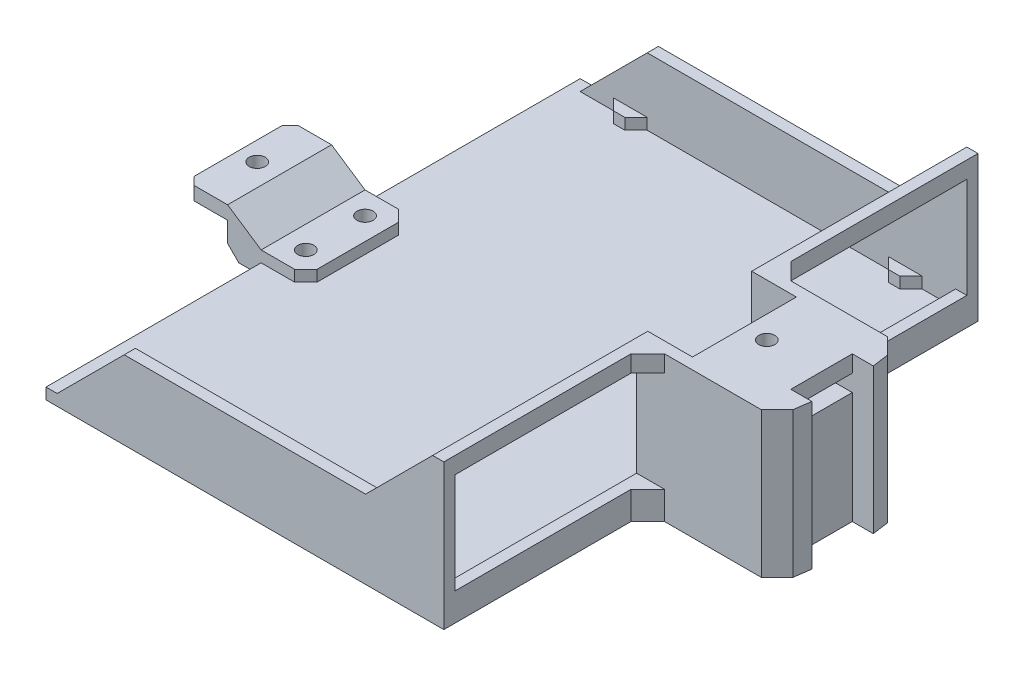
SolidWorks part; units mm, degrees
ref_plane "Front Plane" through (0, 0, 0) normal (0, 0, 1) x (1, 0, 0)
ref_plane "Top Plane" through (0, 0, 0) normal (0, 1, 0) x (1, 0, 0)
ref_plane "Right Plane" through (0, 0, 0) normal (1, 0, 0) x (0, 0, -1)
sketch "Sketch1" plane through (0, 0, 0) normal (0, 1, 0) x (1, 0, 0)
  line L0 (-1000, 0) -> (49000, 0) construction
  line L1 (6.985, -70.358) -> (-6.985, -70.358)
  line L6 (70.358, 6.985) -> (75.1332, 6.985)
  line L7 (70.358, 6.985) -> (70.358, -6.985)
  line L8 (70.358, -6.985) -> (75.1332, -6.985)
  line L9 (75.1332, 6.985) -> (75.1332, -6.985)
  line L10 (6.985, -70.358) -> (6.985, -75.1332)
  line L11 (6.985, -75.1332) -> (-6.985, -75.1332)
  line L12 (-6.985, -70.358) -> (-6.985, -75.1332)
  line L13 (-70.358, -6.985) -> (-70.358, 6.985)
  line L14 (-70.358, -6.985) -> (-75.1332, -6.985)
  line L15 (-75.1332, -6.985) -> (-75.1332, 6.985)
  line L16 (-70.358, 6.985) -> (-75.1332, 6.985)
  line L17 (-6.985, 70.358) -> (6.985, 70.358)
  line L18 (-6.985, 70.358) -> (-6.985, 75.1332)
  line L19 (-6.985, 75.1332) -> (6.985, 75.1332)
  line L20 (6.985, 70.358) -> (6.985, 75.1332)
  circle A0 centre (0, 0) radius 75.692 construction
  circle A1 centre (0, 0) radius 76.2 construction
  point P4 (70.358, 0)
  point P11 (0, 0)
  point P31 (0, 0)
  dimension "D1" = 151.384
  dimension "D2" = 152.4
  dimension "D3" = 13.97
  dimension "D4" = 140.716
  dimension "D6" = 4.7752
  dimension "D7" = 4
sketch "Sketch3" plane through (0, 0, 0) normal (0, 1, 0) x (1, 0, 0)
  line L1 (-45.2113, -60.706) -> (45.2113, -60.706)
  line L2 (-45.2113, -60.706) -> (-45.2113, 60.706)
  line L3 (-45.2113, 60.706) -> (45.2113, 60.706)
  line L4 (45.2113, -60.706) -> (45.2113, 60.706)
  line L5 (-45.2113, -60.706) -> (45.2113, 60.706) construction
  line L6 (-45.2113, 60.706) -> (45.2113, -60.706) construction
  circle A0 centre (0, 0) radius 75.692 construction
  point P0 (0, 0)
  dimension "D1" = 121.412
extrude "Boss-Extrude4" add sketch "Sketch3" along normal blind 2.54
sketch "Sketch6" plane through (0, 2.54, 0) normal (0, 1, 0) x (1, 0, 0)
  line L0 (-1000, 0) -> (49000, 0) construction
  line L1 (45.2113, -60.706) -> (45.2113, 60.706) construction
  line L2 (45.2113, 60.706) -> (-45.2113, 60.706) construction
  line L3 (45.2113, -60.706) -> (45.2113, 60.706)
  line L4 (45.2113, 60.706) -> (-45.2113, 60.706)
  line L5 (-45.2113, 60.706) -> (-45.2113, 58.166)
  line L6 (-45.2113, 60.706) -> (-45.2113, -60.706) construction
  line L7 (-45.2113, 58.166) -> (42.6713, 58.166)
  line L8 (42.6713, 58.166) -> (42.6713, -58.166)
  line L10 (-45.2113, -58.166) -> (42.6713, -58.166)
  line L11 (-45.2113, -60.706) -> (-45.2113, -58.166)
  line L12 (45.2113, -60.706) -> (-45.2113, -60.706)
  dimension "D1" = 2.54
  dimension "D2" = 2.54
extrude "Boss-Extrude5" add sketch "Sketch6" along normal blind 30.48
sketch "Sketch7" plane through (0, 0, 60.706) normal (0, 0, 1) x (1, 0, 0)
  line L0 (42.6713, 2.54) -> (-45.2113, 2.54) construction
  line L1 (42.6713, 33.02) -> (42.6713, 2.54) construction
  line L2 (42.6713, 2.54) -> (-45.2113, 2.54) construction
  line L3 (42.6713, 33.02) -> (42.6713, 2.54) construction
  line L4 (0, -1000) -> (0, 49000) construction
  line L5 (-957.3287, 17.78) -> (49042.6713, 17.78) construction
  line L6 (-42.6713, 33.02) -> (-42.6713, 2.54) construction
  line L7 (-42.6713, 2.54) -> (-27.4313, 17.78)
  line L8 (-27.4313, 17.78) -> (27.4313, 17.78)
  line L9 (27.4313, 17.78) -> (42.6713, 33.02)
  line L10 (42.6713, 33.02) -> (-45.2113, 33.02)
  line L11 (-45.2113, 33.02) -> (-45.2113, 2.54)
  line L12 (-45.2113, 2.54) -> (-42.6713, 2.54)
  point P9 (42.6713, 17.78)
  dimension "D1" = 45
  dimension "D2" = 45
extrude "Cut-Extrude2" cut sketch "Sketch7" against normal through all
sketch "Sketch8" plane through (0, 0, 0) normal (0, 1, 0) x (1, 0, 0)
  line L0 (-1000, 0) -> (49000, 0) construction
  line L1 (45.2113, 14.351) -> (71.0099, 14.351)
  line L2 (45.2113, -60.706) -> (45.2113, 60.706) construction
  line L3 (71.0099, 14.351) -> (74.603, 10.7579)
  line L4 (74.603, 10.7579) -> (75.1332, 6.985)
  line L5 (75.1332, 6.985) -> (70.358, 6.985)
  line L6 (70.358, 6.985) -> (70.358, -6.985)
  line L7 (45.2113, 14.351) -> (45.2113, -14.351)
  line L8 (45.2113, -14.351) -> (71.0099, -14.351)
  line L9 (71.0099, -14.351) -> (74.603, -10.7579)
  line L10 (74.603, -10.7579) -> (75.1332, -6.985)
  line L11 (75.1332, -6.985) -> (70.358, -6.985)
  line L13 (70.358, 6.985) -> (70.358, -6.985) construction
  line L14 (70.358, 6.985) -> (75.1332, 6.985) construction
  point P13 (45.2113, 0)
  point P17 (70.358, 0)
  dimension "D1" = 82
  dimension "D2" = 135
  dimension "D3" = 28.702
  dimension "D4" = 3.81
extrude "Boss-Extrude6" add sketch "Sketch8" along normal up to surface (33.02 mm away) up to face at (43.518, 33.02, 0)
sketch "Sketch9" plane through (0, 33.02, 0) normal (0, 1, 0) x (1, 0, 0)
  line L0 (-1000, 0) -> (49000, 0) construction
  line L1 (52.8313, -11.811) -> (52.8313, 11.811)
  line L2 (52.8313, 11.811) -> (42.6713, 11.811)
  line L3 (42.6713, 58.166) -> (42.6713, -58.166) construction
  line L4 (42.6713, 11.811) -> (42.6713, -11.811)
  line L5 (52.8313, -11.811) -> (42.6713, -11.811)
  line L6 (71.0099, 14.351) -> (45.2113, 14.351) construction
  point P10 (42.6713, 0)
  point P11 (52.8313, 0)
  dimension "D1" = 10.16
  dimension "D2" = 2.54
extrude "Cut-Extrude3" cut sketch "Sketch9" against normal offset from surface (27.94 mm away) 2.54 up to face at (-21.9706, 2.54, 0)
sketch "Sketch11" plane through (0, 2.54, 0) normal (0, 1, 0) x (1, 0, 0)
  line L5 (35.0513, 58.166) -> (27.4313, 58.166)
  line L6 (-42.6713, 58.166) -> (42.6713, 58.166) construction
  line L7 (27.4313, 58.166) -> (29.9713, 55.626)
  line L8 (29.9713, 55.626) -> (32.5113, 55.626)
  line L9 (32.5113, 55.626) -> (35.0513, 58.166)
  line L10 (42.6713, 58.166) -> (42.6713, -58.166) construction
  line L11 (-1000, 0) -> (49000, 0) construction
  line L12 (0, -1000) -> (0, 49000) construction
  line L13 (-29.9713, 55.626) -> (-32.5113, 55.626)
  line L14 (-27.4313, 58.166) -> (-29.9713, 55.626)
  line L15 (-35.0513, 58.166) -> (-27.4313, 58.166)
  line L16 (-32.5113, 55.626) -> (-35.0513, 58.166)
  line L17 (29.9713, -55.626) -> (32.5113, -55.626)
  line L18 (27.4313, -58.166) -> (29.9713, -55.626)
  line L19 (35.0513, -58.166) -> (27.4313, -58.166)
  line L20 (32.5113, -55.626) -> (35.0513, -58.166)
  line L21 (-27.4313, -58.166) -> (-29.9713, -55.626)
  line L22 (-35.0513, -58.166) -> (-27.4313, -58.166)
  line L23 (-32.5113, -55.626) -> (-35.0513, -58.166)
  line L24 (-29.9713, -55.626) -> (-32.5113, -55.626)
  dimension "D1" = 45
  dimension "D2" = 45
  dimension "D3" = 2.54
  dimension "D4" = 2.54
  dimension "D5" = 7.62
extrude "Boss-Extrude7" add sketch "Sketch11" along normal up to surface (2.54 mm away) up to face at (47.7513, 5.08, 0)
sketch "Sketch12" plane through (52.8313, 0, 0) normal (-1, 0, 0) x (0, 0, 1)
  line L0 (11.811, 5.08) -> (11.811, 33.02) construction
  line L1 (11.811, 29.21) -> (-11.811, 29.21)
  line L2 (11.811, 29.21) -> (11.811, 25.4)
  line L3 (11.811, 25.4) -> (-11.811, 25.4)
  line L4 (-11.811, 29.21) -> (-11.811, 25.4)
  line L5 (-11.811, 5.08) -> (-11.811, 33.02) construction
  line L6 (11.811, 33.02) -> (-11.811, 33.02) construction
  dimension "D1" = 3.81
  dimension "D2" = 3.81
extrude "Cut-Extrude4" cut sketch "Sketch12" against normal blind 10.16
sketch "Sketch13" plane through (62.9913, 0, 0) normal (-1, 0, 0) x (0, 0, 1)
  line L0 (11.811, 29.21) -> (-11.811, 29.21) construction
  line L1 (-6.985, 29.21) -> (6.985, 29.21)
  line L2 (-6.985, 29.21) -> (-6.985, 25.4)
  line L3 (-6.985, 25.4) -> (6.985, 25.4)
  line L4 (6.985, 29.21) -> (6.985, 25.4)
  line L5 (-6.985, 33.02) -> (-6.985, 0) construction
  line L6 (-11.811, 25.4) -> (11.811, 25.4) construction
  line L7 (6.985, 33.02) -> (6.985, 0) construction
extrude "Cut-Extrude5" cut sketch "Sketch13" against normal through all
sketch "Sketch15" plane through (0, 0, 0) normal (0, 0, 1) x (1, 0, 0)
  line L0 (0, -1000) -> (0, 49000) construction
  line L2 (62.9913, 29.21) -> (62.9913, 25.4) construction
  line L3 (62.9913, 25.4) -> (52.8313, 25.4) construction
  line L4 (62.9913, 29.21) -> (52.8313, 29.21) construction
  line L5 (62.9913, 25.4) -> (52.8313, 25.4) construction
  line L6 (62.9913, 29.21) -> (62.9913, 25.4) construction
  line L7 (62.9913, 29.21) -> (52.8313, 29.21) construction
  line L8 (-62.9913, 29.21) -> (-52.8313, 29.21) construction
  line L9 (-62.9913, 29.21) -> (-62.9913, 25.4) construction
  line L10 (-62.9913, 25.4) -> (-52.8313, 25.4) construction
  line L11 (-998.1426, 17.78) -> (49001.8574, 17.78) construction
  line L13 (-62.9913, 10.16) -> (-52.8313, 10.16)
  line L14 (-62.9913, 6.35) -> (-62.9913, 10.16)
  line L15 (-62.9913, 6.35) -> (-52.8313, 6.35)
  line L16 (-27.4313, 17.78) -> (27.4313, 17.78) construction
  line L17 (-52.8313, 6.35) -> (-52.8313, 0)
  line L18 (-52.8313, 0) -> (-45.2113, 0)
  line L19 (-45.2113, 0) -> (-45.2113, 2.54)
  line L20 (-45.2113, 2.54) -> (-35.0513, 2.54)
  line L21 (-35.0513, 2.54) -> (-42.6713, 2.54) construction
  line L23 (-35.0513, 2.54) -> (-35.0513, 5.08)
  line L24 (-35.0513, 5.08) -> (-45.2113, 5.08)
  line L25 (-45.2113, 5.08) -> (-52.8313, 10.16)
  line L26 (-27.4313, 5.08) -> (-35.0513, 5.08) construction
  line L27 (52.8313, 5.08) -> (42.6713, 5.08) construction
  line L28 (52.8313, 5.08) -> (42.6713, 5.08) construction
extrude "Boss-Extrude9" add sketch "Sketch15" against normal up to surface and the other way up to surface up to face at (52.8313, 23.1775, -11.811) other way up to face at (52.8313, 23.1775, 11.811)
hole_wizard "CBORE for #6 Pan Head Machine Screw1" positions "Sketch16" profile "Sketch17" counterbore size "#6" standard "ANSI Inch" end condition through all
sketch "Sketch16" plane through (0, 0, 0) normal (0, -1, 0) x (-1, 0, 0)
  line L0 (-47.7513, -988.189) -> (-47.7513, 49011.811) construction
  line L1 (-52.8313, 11.811) -> (-42.6713, 11.811) construction
  line L2 (-1000, 0) -> (49000, 0) construction
  line L3 (40.1313, -988.189) -> (40.1313, 49011.811) construction
  line L4 (45.2113, 11.811) -> (35.0513, 11.811) construction
  line L5 (-1047.7513, 6.731) -> (48952.2487, 6.731) construction
  line L6 (-1047.7513, -6.731) -> (48952.2487, -6.731) construction
  line L7 (-52.8313, 11.811) -> (-42.6713, 1.651) construction
  line L8 (-42.6713, 11.811) -> (-42.6713, -11.811) construction
  point P0 (-47.7513, 6.731)
  point P7 (-47.7513, 11.811)
  point P18 (-47.7513, -6.731)
  point P24 (40.1313, 11.811)
  point P34 (40.1313, 6.731)
  point P36 (40.1313, -6.731)
  dimension "D1" = 45
sketch "Sketch17" plane through (47.7513, 0, -6.731) normal (1, 0, 0) x (0, 0, -1)
  line L0 (0, 0) -> (0, 33.02)
  line L1 (0, 33.02) -> (1.8288, 33.02)
  line L3 (1.8288, 33.02) -> (1.8288, 2.4638)
  line L4 (1.8288, 2.4638) -> (3.7706, 2.4638)
  line L5 (3.7706, 2.4638) -> (3.7706, 0)
  line L7 (3.7706, 0) -> (0, 0)
  line L11 (0, -6.35) -> (0, 107.95) construction
  dimension "Thru Hole Dia." = 3.6576
  dimension "Thru Hole Depth" = 33.02
  dimension "C'Bore Dia." = 7.5413
  dimension "C'Bore Depth" = 2.4638
hole_wizard "#6 Clearance Hole1" positions "Sketch19" profile "Sketch20" hole size "#6" standard "ANSI Inch" end condition through all
sketch "Sketch19" plane through (0, 33.02, 0) normal (0, 1, 0) x (1, 0, 0)
  line L0 (-1000, 0) -> (49000, 0) construction
  line L1 (0, -1000) -> (0, 49000) construction
  line L2 (57.9113, -988.189) -> (57.9113, 49011.811) construction
  line L3 (62.9913, 11.811) -> (52.8313, 11.811) construction
  point P6 (57.9113, 0)
  point P13 (-57.9113, 0)
  point P20 (57.9113, 11.811)
sketch "Sketch20" plane through (-57.9113, 33.02, 0) normal (1, 0, 0) x (0, 0, 1)
  line L0 (0, 0) -> (0, 33.02)
  line L1 (0, 33.02) -> (1.8288, 33.02)
  line L2 (1.8288, 33.02) -> (1.8288, 0)
  line L5 (1.8288, 0) -> (0, 0)
  line L11 (0, -6.35) -> (0, 107.95) construction
  dimension "Thru Hole Dia." = 3.6576
  dimension "Thru Hole Depth" = 33.02
sketch "Sketch21" plane through (42.6713, 0, 0) normal (-1, 0, 0) x (0, 0, 1)
  line L0 (-1058.166, 17.78) -> (48941.834, 17.78) construction
  line L1 (-58.166, 33.02) -> (-58.166, 2.54) construction
  line L2 (0, -1000) -> (0, 49000) construction
  line L3 (-11.811, 0) -> (11.811, 0) construction
  line L9 (-1008.4655, 5.08) -> (48991.5345, 5.08) construction
  line L10 (-58.166, 6.35) -> (-58.166, 29.21)
  line L11 (-11.811, 5.08) -> (11.811, 5.08) construction
  line L14 (-58.166, 29.21) -> (-14.351, 29.21)
  line L15 (-14.351, 29.21) -> (-14.351, 6.35)
  line L18 (-58.166, 6.35) -> (-14.351, 6.35)
  line L20 (58.166, 29.21) -> (14.351, 29.21)
  line L21 (58.166, 6.35) -> (58.166, 29.21)
  line L22 (58.166, 6.35) -> (14.351, 6.35)
  line L23 (14.351, 29.21) -> (14.351, 6.35)
  line L24 (-58.166, 33.02) -> (-58.166, 17.78) construction
  line L25 (-14.351, 33.02) -> (-14.351, 0) construction
  point P5 (-58.166, 17.78)
  point P10 (0, 0)
  point P19 (-14.351, 17.78)
  point P20 (-58.166, 17.78)
  dimension "D1" = 1.27
extrude "Cut-Extrude6" cut sketch "Sketch21" against normal through all
chamfer "Chamfer1" distance 2.54 angle 45 5 edges at (-62.9913, 8.255, -11.811) (-62.9913, 8.255, 11.811) (-35.0513, 3.81, 11.811) (-35.0513, 3.81, -11.811) (-52.8313, 0, 0)
chamfer "Chamfer2" distance 3.81 angle 45 4 edges at (45.2113, 3.175, -14.351) (45.2113, 3.175, 14.351) (45.2113, 31.115, -14.351) (45.2113, 31.115, 14.351)
sketch "Sketch23" plane through (0, 6.35, 0) normal (0, -1, 0) x (1, 0, 0)
  line L0 (-62.9913, -9.271) -> (-62.9913, 9.271) construction
  line L1 (-52.8313, 11.811) -> (-62.9913, 11.811)
  line L2 (-52.8313, 11.811) -> (-52.8313, -11.811)
  line L3 (-52.8313, -11.811) -> (-62.9913, -11.811)
  line L4 (-62.9913, 11.811) -> (-62.9913, -11.811)
  line L5 (-60.4513, -11.811) -> (-52.8313, -11.811) construction
extrude "Cut-Extrude8" cut sketch "Sketch23" against normal blind 0.762
chamfer "Chamfer3" distance 0.762 angle 45 2 edges at (-62.9913, 7.112, 0) (-62.9913, 10.16, 0)
